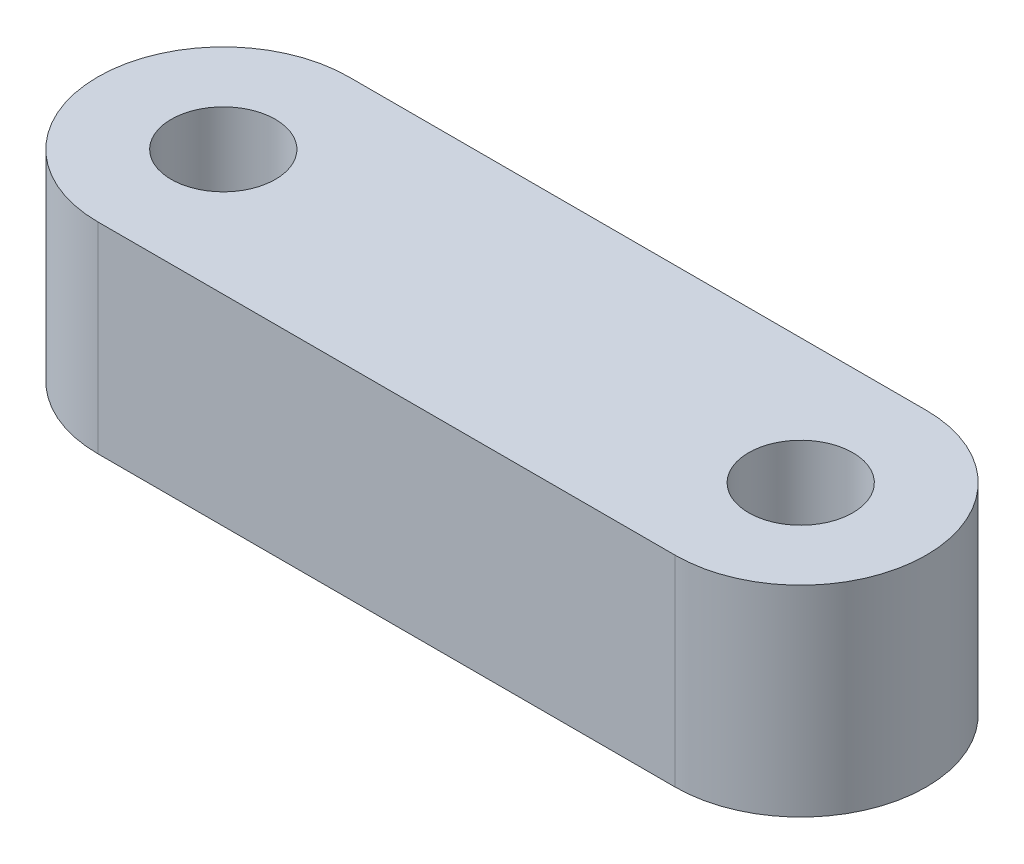
SolidWorks part; units mm, degrees
ref_plane "前视基准面" through (0, 0, 0) normal (0, 0, 1) x (1, 0, 0)
ref_plane "上视基准面" through (0, 0, 0) normal (0, 1, 0) x (1, 0, 0)
ref_plane "右视基准面" through (0, 0, 0) normal (1, 0, 0) x (0, 0, -1)
other "Configuration Table"
sketch "草图1" plane through (0, 0, 0) normal (0, 1, 0) x (1, 0, 0)
  line L0 (0, 0) -> (23, 0) construction
  line L1 (0, 5) -> (23, 5)
  line L2 (0, -5) -> (23, -5)
  arc A0 (0, 5) -> (0, -5) centre (0, 0) ccw
  arc A1 (23, -5) -> (23, 5) centre (23, 0) ccw
  point P3 (11.5, 0)
  dimension "D1" = 10
  dimension "D2" = 23
extrude "凸台-拉伸1" add sketch "草图1" along normal blind 8
sketch "草图2" plane through (0, 0, 0) normal (0, 0, 1) x (1, 0, 0)
  line L0 (0, 0) -> (0, 8) construction
  line L1 (0, 8) -> (-2.075, 8)
  line L2 (0, 8) -> (-5, 8) construction
  line L3 (-2.075, 8) -> (-2.075, 3.5)
  line L4 (-2.075, 3.5) -> (-3.75, 3.5)
  line L5 (-3.75, 3.5) -> (-3.75, 0)
  line L6 (-5, 0) -> (0, 0) construction
  line L7 (-3.75, 0) -> (0, 0)
  line L8 (0, 0) -> (0, 8)
  dimension "D1" = 4.15
  dimension "D2" = 3.5
  dimension "D3" = 7.5
revolve "切除-旋转1" cut sketch "草图2" angle 360 about L0
sketch "草图3" plane through (0, 0, 0) normal (0, 0, 1) x (1, 0, 0)
  line L0 (23, 0) -> (23, 8) construction
  line L1 (23, 8) -> (20.925, 8)
  line L2 (0, 8) -> (23, 8) construction
  line L3 (20.925, 8) -> (20.925, 3.5)
  line L4 (20.925, 3.5) -> (19.25, 3.5)
  line L5 (19.25, 3.5) -> (19.25, 0)
  line L6 (0, 0) -> (23, 0) construction
  line L7 (19.25, 0) -> (23, 0)
  line L8 (23, 0) -> (23, 8)
  dimension "D1" = 4.15
  dimension "D2" = 7.5
  dimension "D3" = 3.5
revolve "切除-旋转2" cut sketch "草图3" angle 360 about L0
